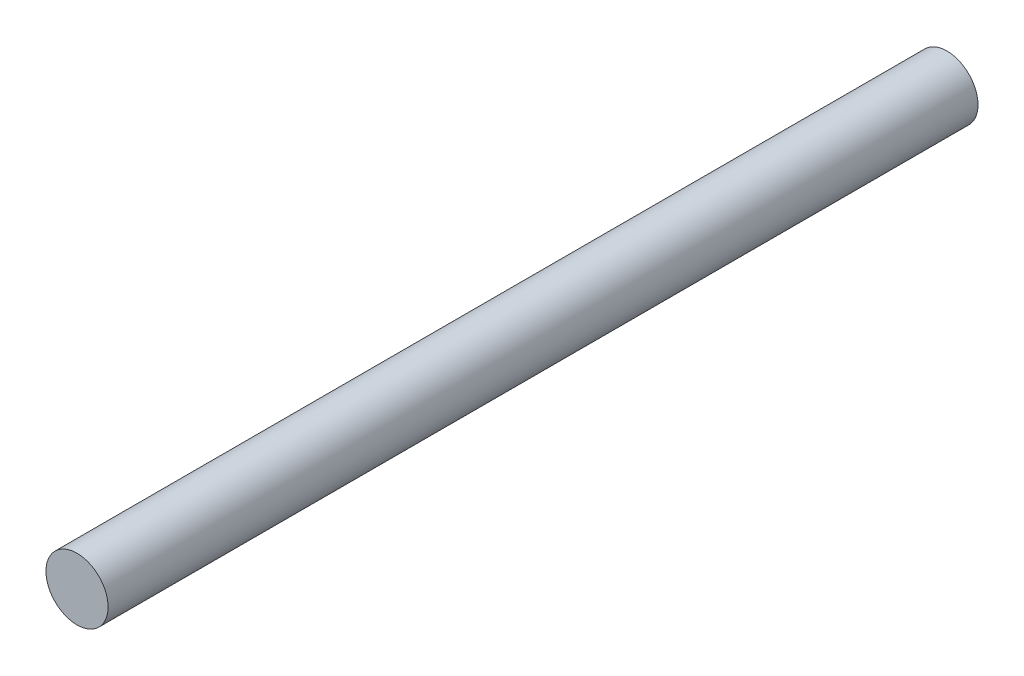
SolidWorks part; units mm, degrees
ref_plane "Front Plane" through (0, 0, 0) normal (0, 0, 1) x (1, 0, 0)
ref_plane "Top Plane" through (0, 0, 0) normal (0, 1, 0) x (1, 0, 0)
ref_plane "Right Plane" through (0, 0, 0) normal (1, 0, 0) x (0, 0, -1)
sketch "Sketch1" plane through (0, 0, 0) normal (0, 0, 1) x (1, 0, 0)
  circle A0 centre (0, 0) radius 5
  dimension "D1" = 10
extrude "Boss-Extrude1" add sketch "Sketch1" along normal blind 140
